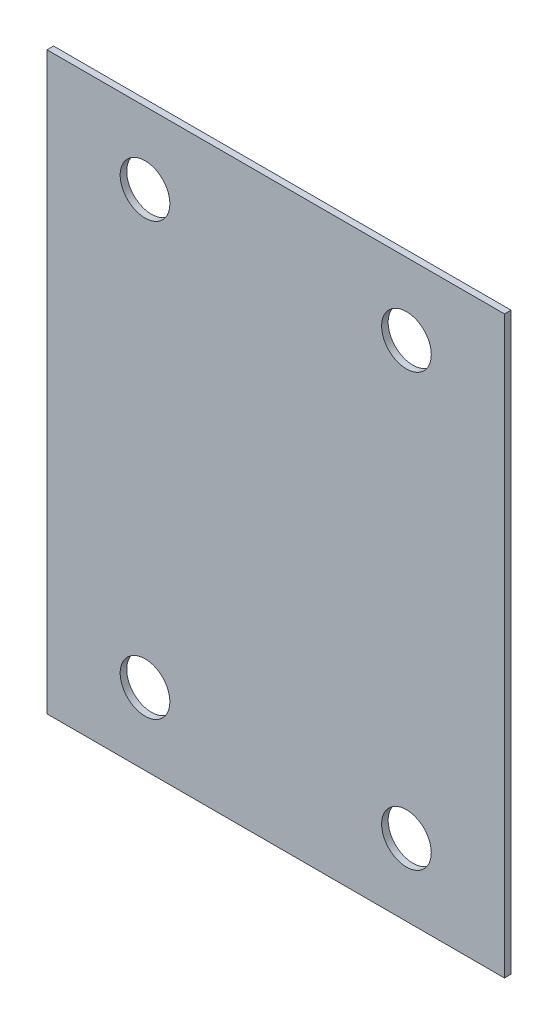
SolidWorks part; units mm, degrees
ref_plane "Спереди" through (0, 0, 0) normal (0, 0, 1) x (1, 0, 0)
ref_plane "Сверху" through (0, 0, 0) normal (0, 1, 0) x (1, 0, 0)
ref_plane "Справа" through (0, 0, 0) normal (1, 0, 0) x (0, 0, -1)
sketch "Эскиз1" plane through (0, 0, 0) normal (0, 0, 1) x (1, 0, 0)
  line L0 (175, -220) -> (175, 220)
  line L1 (175, 220) -> (-175, 220)
  line L2 (-175, 220) -> (-175, -220)
  line L3 (-175, -220) -> (175, -220)
  circle A4 centre (-100, 165) radius 19
  circle A5 centre (100, 165) radius 19
  circle A6 centre (100, -165) radius 19
  circle A7 centre (-100, -165) radius 19
extrude "Бобышка-Вытянуть1" add sketch "Эскиз1" along normal blind 5
